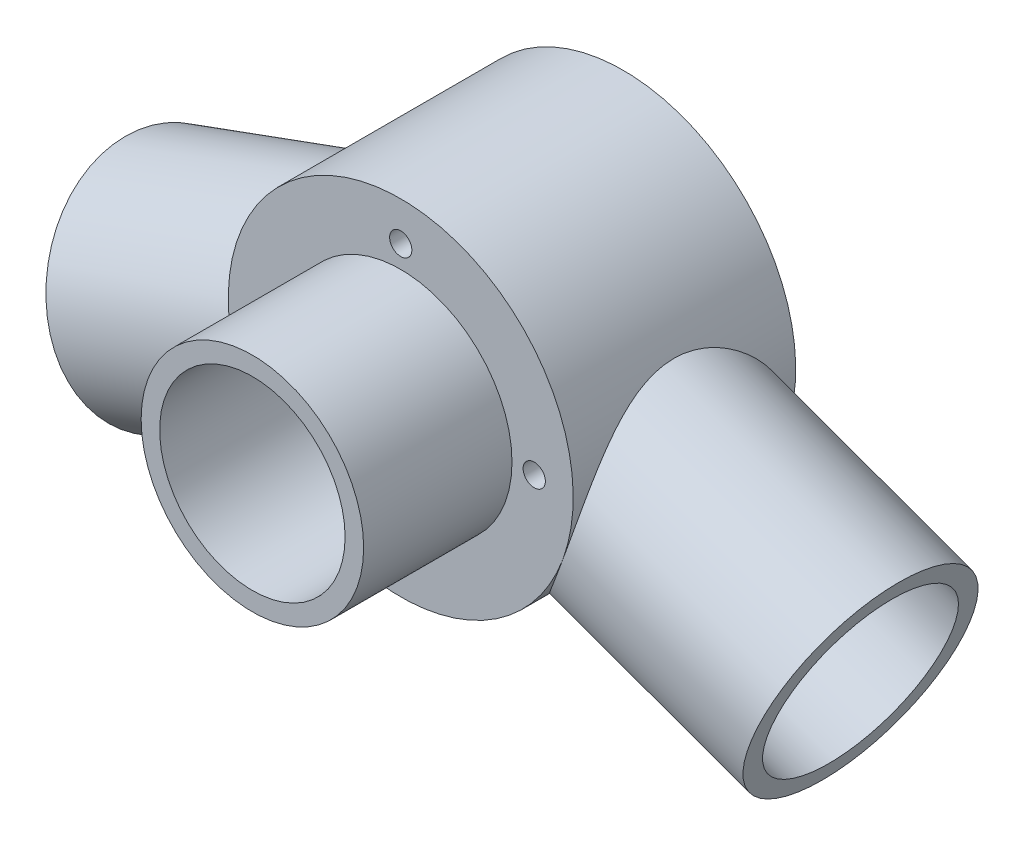
SolidWorks part; units mm, degrees
ref_plane "Alzado" through (0, 0, 0) normal (0, 0, 1) x (1, 0, 0)
ref_plane "Planta" through (0, 0, 0) normal (0, 1, 0) x (1, 0, 0)
ref_plane "Vista lateral" through (0, 0, 0) normal (1, 0, 0) x (0, 0, -1)
sketch "Croquis1" plane through (0, 0, 0) normal (0, 0, 1) x (1, 0, 0)
  circle A0 centre (0, 0) radius 15
  circle A1 centre (0, 0) radius 12.5
  dimension "D1" = 30
  dimension "D2" = 25
extrude "Saliente-Extruir1" add sketch "Croquis1" against normal blind 20
sketch3d "Croquis3D3"
  line L0 (0, 0, 0) -> (0, 0, -60) construction
  line L1 (0, 0, -60) -> (40, 0, -60) construction
  line L2 (40, 0, -60) -> (40, 0, -35) construction
  line L3 (40, 0, -35) -> (0, 0, -35) construction
  line L4 (0, 0, -35) -> (-40, 0, -35) construction
  line L5 (-40, 0, -35) -> (-40, 0, -60.0108) construction
  line L6 (-40, 0, -60.0108) -> (0, 0, -60) construction
  line L7 (0, 0, -35) -> (-46.9846, -17.101, -35) construction
  line L8 (0, 0, -35) -> (46.9846, -17.101, -35) construction
  line L9 (0, 0, 0) -> (0, -10.0221, 0) construction
  line L10 (46.9846, -17.101, -35) -> (46.9846, 0, -35) construction
  line L11 (-46.9846, -17.101, -35) -> (-46.9846, 0, -35) construction
  dimension "D2" = 25
  dimension "D1" = 60
  dimension "D3" = 40
  dimension "D4" = 140
  dimension "D5" = 50
sketch "Croquis8" plane through (0, 0, -20) normal (0, 0, -1) x (-1, 0, 0)
  line L0 (0, 0) -> (0, 18) construction
  line L1 (0, 0) -> (-18, 0) construction
  line L2 (0, 0) -> (-40, 0) construction
  line L3 (0, 0) -> (0, -18) construction
  line L4 (0, 0) -> (18, 0) construction
  line L5 (0, 0) -> (40, 0) construction
  circle A0 centre (0, 0) radius 23.25
  circle A1 centre (0, 18) radius 1.5
  circle A2 centre (18, 0) radius 1.5
  circle A3 centre (0, -18) radius 1.5
  circle A4 centre (-18, 0) radius 1.5
  dimension "D1" = 46.5
  dimension "D3" = 3
  dimension "D2" = 18
extrude "Saliente-Extruir2" add sketch "Croquis8" along normal blind 30
ref_plane "Plano2" through (46.9846, -17.101, -35) normal (0.9397, -0.342, 0) x (0, 0, -1)
sketch "Croquis6" plane through (46.9846, -17.101, -35) normal (0.9397, -0.342, 0) x (0, 0, -1)
  circle A0 centre (0, 0) radius 15
  circle A1 centre (0, 0) radius 12.5
  dimension "D1" = 30
  dimension "D2" = 25
ref_plane "Plano3" through (-46.9846, -17.101, -35) normal (-0.9397, -0.342, 0) x (0, 0, 1)
sketch "Croquis7" plane through (-46.9846, -17.101, -35) normal (-0.9397, -0.342, 0) x (0, 0, 1)
  circle A0 centre (0, 0) radius 15
  circle A1 centre (0, 0) radius 12.5
  dimension "D1" = 30
  dimension "D2" = 25
extrude "Saliente-Extruir4" add sketch "Croquis6" against normal up to surface (32.2359 mm away)
extrude "Saliente-Extruir5" add sketch "Croquis7" against normal up to surface (32.2359 mm away)
sketch "Croquis9" plane through (0, 0, -20) normal (0, 0, 1) x (1, 0, 0)
  circle A0 centre (0, 0) radius 12.5
  dimension "D1" = 25
extrude "Cortar-Extruir1" cut sketch "Croquis9" against normal through all
